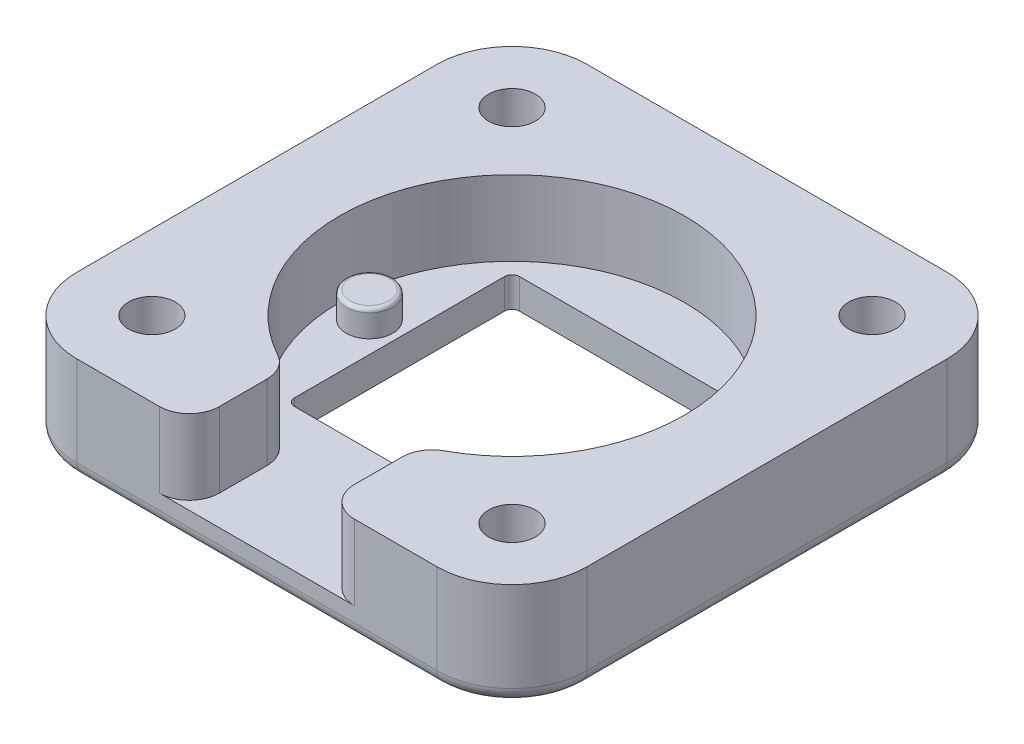
SolidWorks part; units mm, degrees
ref_plane "Front Plane" through (0, 0, 0) normal (0, 0, 1) x (1, 0, 0)
ref_plane "Top Plane" through (0, 0, 0) normal (0, 1, 0) x (1, 0, 0)
ref_plane "Right Plane" through (0, 0, 0) normal (1, 0, 0) x (0, 0, -1)
sketch "Sketch1" plane through (0, 0, 0) normal (0, 1, 0) x (1, 0, 0)
  line L1 (-17.6093, 13.1991) -> (16.3907, 13.1991)
  line L2 (-17.6093, 13.1991) -> (-17.6093, -20.8009)
  line L3 (-17.6093, -20.8009) -> (16.3907, -20.8009)
  line L4 (16.3907, 13.1991) -> (16.3907, -20.8009)
  dimension "D1" = 34
  dimension "D2" = 34
extrude "Boss-Extrude1" add sketch "Sketch1" along normal blind 7
sketch "Sketch2" plane through (0, 7, 0) normal (0, 1, 0) x (1, 0, 0)
  line L0 (-0.6093, 13.1991) -> (-0.6093, -34.5004) construction
  line L1 (16.3907, 13.1991) -> (-17.6093, 13.1991) construction
  line L2 (-17.6093, -3.8009) -> (26.5191, -3.8009) construction
  line L4 (-17.6093, 13.1991) -> (-17.6093, -20.8009) construction
  circle A0 centre (-0.6093, -3.8009) radius 11.5
  point P7 (-0.6093, -3.8009)
  dimension "D1" = 23
extrude "Cut-Extrude1" cut sketch "Sketch2" against normal blind 5
sketch "Sketch3" plane through (0, 7, 0) normal (0, 1, 0) x (1, 0, 0)
  line L0 (16.3907, 13.1991) -> (-17.6093, 13.1991) construction
  line L3 (-17.6093, 13.1991) -> (-17.6093, -20.8009) construction
  line L4 (-0.6093, 13.1991) -> (-0.6093, -21.9345) construction
  line L5 (-17.6093, -3.8009) -> (18.9364, -3.8009) construction
  circle A0 centre (-12.6093, 8.1991) radius 1.5621
  circle A1 centre (-12.6093, -15.8009) radius 1.5621
  circle A2 centre (11.3907, -15.8009) radius 1.5621
  circle A3 centre (11.3907, 8.1991) radius 1.5621
  dimension "D1" = 5
  dimension "D2" = 5
extrude "Cut-Extrude2" cut sketch "Sketch3" against normal through all
sketch "Sketch4" plane through (0, 7, 0) normal (0, 1, 0) x (1, 0, 0)
  line L0 (-0.6093, 13.1991) -> (-0.6093, -22.9594) construction
  line L1 (16.3907, 13.1991) -> (-17.6093, 13.1991) construction
  line L3 (-5.1093, -10.3426) -> (3.8907, -10.3426)
  line L4 (-5.1093, -10.3426) -> (-5.1093, -23.2421)
  line L5 (-5.1093, -23.2421) -> (3.8907, -23.2421)
  line L6 (3.8907, -10.3426) -> (3.8907, -23.2421)
  dimension "D1" = 9
  dimension "D2" = 4.5
extrude "Cut-Extrude3" cut sketch "Sketch4" against normal blind 5
sketch "Sketch5" plane through (0, 0, 0) normal (0, -1, 0) x (1, 0, 0)
  circle A0 centre (-12.6093, 15.8009) radius 2.6
  circle A1 centre (11.3907, 15.8009) radius 2.6
  circle A2 centre (-12.6093, -8.1991) radius 2.6
  circle A3 centre (11.3907, -8.1991) radius 2.6
extrude "Cut-Extrude4" cut sketch "Sketch5" against normal blind 4
fillet "Fillet1" radius 5 4 edges at (16.3907, 3.5, 20.8009) (16.3907, 3.5, -13.1991) (-17.6093, 3.5, -13.1991) (-17.6093, 3.5, 20.8009)
fillet "Fillet2" radius 1 12 edges at (14.9262, 0, -11.7347) (-0.6093, 0, -13.1991) (-16.1449, 0, -11.7347) (-17.6093, 0, 3.8009) (-16.1449, 0, 19.3364) (-0.6093, 0, 20.8009) (14.9262, 0, 19.3364) (16.3907, 0, 3.8009) (-12.6093, 0, 13.2009) (11.3907, 0, -10.7991) (-12.6093, 0, -10.7991) (11.3907, 0, 13.2009)
fillet "Fillet3" radius 2 4 edges at (-5.1093, 4.5, 14.3839) (3.8907, 4.5, 14.3839) (-5.1093, 4.5, 20.8009) (3.8907, 4.5, 20.8009)
sketch "Sketch6" plane through (0, 0, 0) normal (0, -1, 0) x (1, 0, 0)
  line L0 (-0.6093, 19.8009) -> (-0.6093, -12.1991) construction
  line L1 (11.3907, 19.8009) -> (-12.6093, 19.8009) construction
  line L2 (-12.6093, -12.1991) -> (11.3907, -12.1991) construction
  line L3 (-16.6093, 3.8009) -> (15.3907, 3.8009) construction
  line L4 (-16.6093, 15.8009) -> (-16.6093, -8.1991) construction
  line L5 (15.3907, -8.1991) -> (15.3907, 15.8009) construction
  line L7 (-8.1093, 11.3009) -> (6.8907, 11.3009)
  line L8 (-8.1093, 11.3009) -> (-8.1093, -3.6991)
  line L9 (-8.1093, -3.6991) -> (6.8907, -3.6991)
  line L10 (6.8907, 11.3009) -> (6.8907, -3.6991)
  dimension "D1" = 15
  dimension "D2" = 15
  dimension "D3" = 7.5
  dimension "D4" = 7.5
extrude "Cut-Extrude5" cut sketch "Sketch6" against normal blind 2
sketch "Sketch7" plane through (0, 2, 0) normal (0, 1, 0) x (1, 0, 0)
  line L0 (6.8907, -3.8009) -> (-8.1093, -3.8009) construction
  line L1 (6.8907, 3.6991) -> (6.8907, -11.3009) construction
  line L2 (-8.1093, -11.3009) -> (-8.1093, 3.6991) construction
  line L3 (-0.6093, -11.3009) -> (-0.6093, 3.6991) construction
  line L4 (6.8907, -11.3009) -> (-8.1093, -11.3009) construction
  line L5 (-8.1093, 3.6991) -> (6.8907, 3.6991) construction
  line L6 (8.8907, -3.8009) -> (-10.1093, -3.8009) construction
  circle A0 centre (-0.6093, -3.8009) radius 9.5
  circle A1 centre (8.8907, -3.8009) radius 1.55
  circle A3 centre (-10.1093, -3.8009) radius 1.55
  circle A5 centre (-0.6093, -13.3009) radius 1.55 [skipped]
  circle A6 centre (-0.6093, 5.6991) radius 1.55 [skipped]
  point P12 (-0.6093, -3.8009)
  point P27 (-0.6093, -3.8009)
  dimension "D1" = 4
extrude "Boss-Extrude3" add sketch "Sketch7" along normal blind 1.75 contours A0 A1 | A0 A1 | A0 A3 | A0 A3
fillet "Fillet5" radius 0.25 2 edges at (8.8907, 3.75, 5.3509) (-10.1093, 3.75, 5.3509)
fillet "Fillet6" radius 0.5 4 edges at (-8.1093, 1, -3.6991) (6.8907, 1, -3.6991) (-8.1093, 1, 11.3009) (6.8907, 1, 11.3009)
